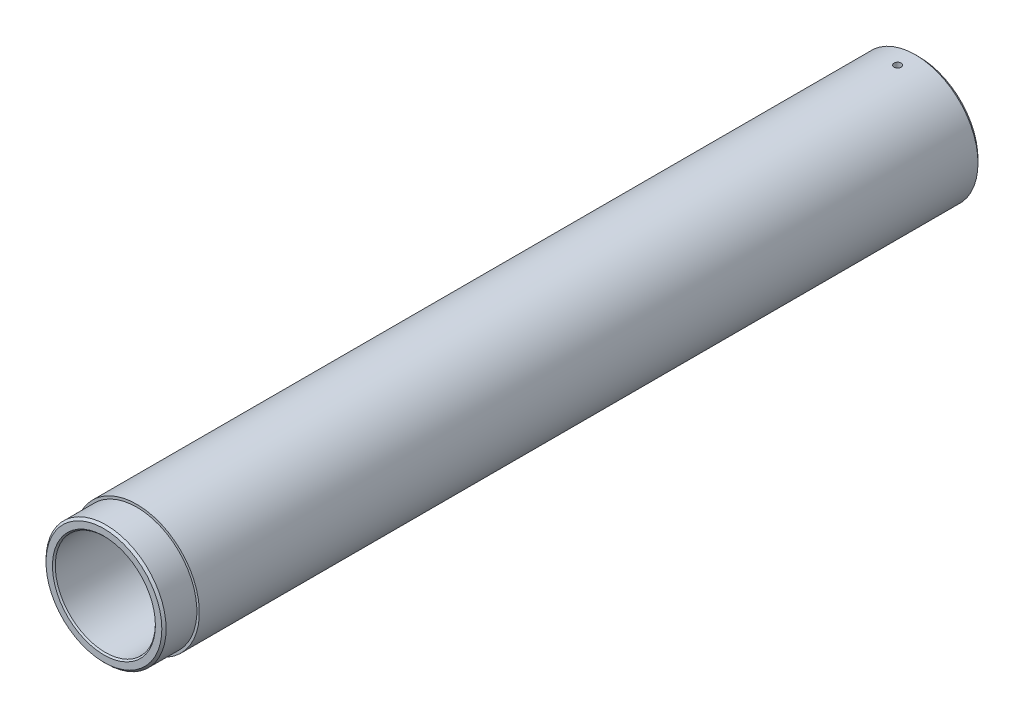
SolidWorks part; units mm, degrees
ref_plane "Front Plane" through (0, 0, 0) normal (0, 0, 1) x (1, 0, 0)
ref_plane "Top Plane" through (0, 0, 0) normal (0, 1, 0) x (1, 0, 0)
ref_plane "Right Plane" through (0, 0, 0) normal (1, 0, 0) x (0, 0, -1)
sketch "Sketch1" plane through (0, 0, 0) normal (0, 0, 1) x (1, 0, 0)
  circle A0 centre (0, 0) radius 70
  circle A1 centre (0, 0) radius 87.5
  dimension "D1" = 140
  dimension "D2" = 175
extrude "Boss-Extrude1" add sketch "Sketch1" along normal mid plane 1140
chamfer "Chamfer1" distance 5 angle 45 1 edges at (87.5, 0, -570)
sketch "Sketch3" plane through (0, 0, 0) normal (1, 0, 0) x (0, 0, -1)
  line L0 (0, 0) -> (-295.5782, 0) construction
  line L1 (-570, 87.5) -> (-570, -87.5) construction
  line L2 (-570, 107.2716) -> (-524, 107.2716)
  line L3 (-570, 107.2716) -> (-570, 84)
  line L4 (-570, 84) -> (-524, 84)
  line L5 (-524, 107.2716) -> (-524, 84)
  dimension "D1" = 46
  dimension "D2" = 168
revolve "Cut-Revolve1" cut sketch "Sketch3" angle 360 about L0
cosmetic thread "Cosmetic Thread1" parameters "D2"=166
chamfer "Chamfer2" distance 3 angle 45 1 edges at (-84, 0, 570)
chamfer "Chamfer3" distance 2 angle 45 1 edges at (70, 0, 570)
sketch "Sketch4" plane through (0, 0, 0) normal (0, 1, 0) x (1, 0, 0)
  line L0 (0, 0) -> (0, 643.3439) construction
  line L1 (70, 570) -> (-70, 570) construction
  circle A0 centre (0, 540) radius 5
  dimension "D1" = 10
  dimension "D2" = 30
extrude "Cut-Extrude1" cut sketch "Sketch4" along normal blind 102
